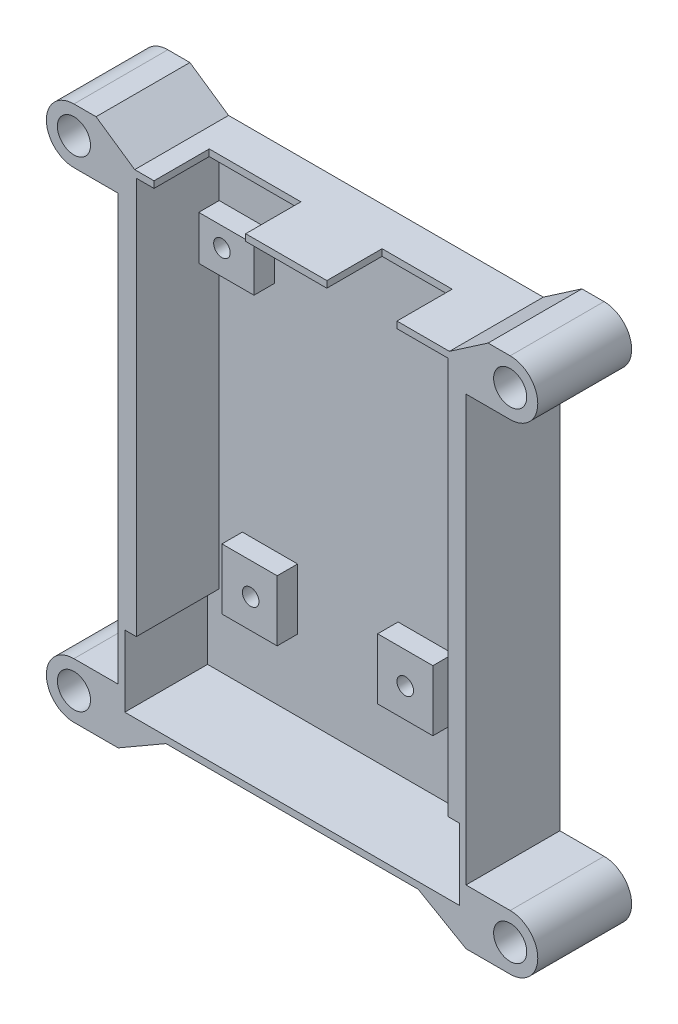
SolidWorks part; units mm, degrees
ref_plane "Front" through (0, 0, 0) normal (0, 0, 1) x (1, 0, 0)
ref_plane "Top" through (0, 0, 0) normal (0, 1, 0) x (1, 0, 0)
ref_plane "Right" through (0, 0, 0) normal (1, 0, 0) x (0, 0, -1)
sketch "草图1" plane through (0, 0, 0) normal (0, 0, 1) x (1, 0, 0)
  line L0 (0, 0) -> (8, 0)
  line L1 (8, 0) -> (8, 77)
  line L2 (8, 77) -> (0, 77)
  line L3 (0, -10) -> (8, -10)
  line L4 (8, -10) -> (16.6603, -5)
  line L5 (16.6603, -5) -> (62.3397, -5)
  line L6 (62.3397, -5) -> (71, -10)
  line L7 (71, -10) -> (79, -10)
  line L8 (79, 0) -> (71, 0)
  line L9 (71, 0) -> (71, 77)
  line L10 (71, 77) -> (79, 77)
  line L11 (0, 87) -> (79, 87)
  arc A0 (0, 0) -> (0, -10) centre (0, -5) ccw
  arc A1 (79, -10) -> (79, 0) centre (79, -5) ccw
  arc A2 (0, 77) -> (0, 87) centre (0, 82) cw
  arc A3 (79, 87) -> (79, 77) centre (79, 82) cw
  dimension "D1" = 5
  dimension "D2" = 5
  dimension "D3" = 5
  dimension "D4" = 8
  dimension "D14" = 63
  dimension "D5" = 8
  dimension "D6" = 8
  dimension "D7" = 8
  dimension "D8" = 5
  dimension "D9" = 5
  dimension "D10" = 63
  dimension "D11" = 92
  dimension "D12" = 30
  dimension "D13" = 30
extrude "凸台-拉伸1" add sketch "草图1" along normal blind 2
sketch "草图2" plane through (0, 0, 2) normal (0, 0, 1) x (1, 0, 0)
  line L0 (79, 87) -> (0, 87) construction
  line L1 (11.3, 81) -> (67.7, 81)
  line L2 (11.3, 81) -> (11.3, 9.1)
  line L3 (11.3, 9.1) -> (67.7, 9.1)
  line L4 (67.7, 81) -> (67.7, 9.1)
  point P4 (39.5, 81)
  point P7 (39.5, 87)
  arc M5 (0, 0) -> (0, -10) centre (0, -5) ccw
  line M6 (0, -10) -> (8, -10)
  line M7 (8, -10) -> (16.6603, -5)
  line M8 (16.6603, -5) -> (62.3397, -5)
  line M9 (62.3397, -5) -> (71, -10)
  line M10 (71, -10) -> (79, -10)
  arc M11 (79, -10) -> (79, 0) centre (79, -5) ccw
  line M12 (79, 0) -> (71, 0)
  line M13 (71, 0) -> (71, 77)
  line M14 (71, 77) -> (79, 77)
  arc M15 (79, 77) -> (79, 87) centre (79, 82) ccw
  line M16 (79, 87) -> (0, 87)
  arc M17 (0, 87) -> (0, 77) centre (0, 82) ccw
  line M18 (0, 77) -> (8, 77)
  line M19 (8, 77) -> (8, 0)
  line M20 (8, 0) -> (0, 0)
  dimension "D1" = 71.9
  dimension "D2" = 56.4
  dimension "D3" = 6
extrude "凸台-拉伸3" add sketch "草图2" along normal blind 15 contours L1 L4 L3 L2 M20 M5 M6 M7 M8 M9 M10 M11 M12 M13 M14 M15 M16 M17 M18 M19
sketch "草图6" plane through (0, 0, 17) normal (0, 0, 1) x (1, 0, 0)
  circle A0 centre (0, 82) radius 3
  circle A1 centre (0, -5) radius 3
  circle A2 centre (79, -5) radius 3
  circle A3 centre (79, 82) radius 3
  dimension "D1" = 6
  dimension "D2" = 6
  dimension "D3" = 6
  dimension "D4" = 6
extrude "切除-拉伸1" cut sketch "草图6" against normal through all
sketch "草图7" plane through (0, 0, 2) normal (0, 0, 1) x (1, 0, 0)
  line L0 (67.7, 61.8) -> (67.7, 69.8)
  line L1 (67.7, 61.8) -> (57.7, 61.8)
  line L2 (67.7, 69.8) -> (57.7, 69.8)
  line L3 (57.7, 61.8) -> (57.7, 69.8)
  line L4 (67.7, 81) -> (67.7, 9.1) construction
  line L5 (11.3, 62) -> (11.3, 70)
  line L6 (11.3, 62) -> (21.3, 62)
  line L7 (11.3, 70) -> (21.3, 70)
  line L8 (21.3, 62) -> (21.3, 70)
  line L9 (11.3, 81) -> (11.3, 9.1) construction
  line L10 (53.7, 9.1) -> (53.7, 20.1)
  line L11 (53.7, 9.1) -> (43.7, 9.1)
  line L12 (53.7, 20.1) -> (43.7, 20.1)
  line L13 (43.7, 9.1) -> (43.7, 20.1)
  line L14 (11.3, 9.1) -> (67.7, 9.1) construction
  line L15 (25.5, 9.1) -> (15.5, 9.1)
  line L16 (25.5, 9.1) -> (25.5, 20.1)
  line L17 (15.5, 9.1) -> (15.5, 20.1)
  line L18 (25.5, 20.1) -> (15.5, 20.1)
  line L19 (11.3, 81) -> (67.7, 81) construction
  dimension "D1" = 10
  dimension "D2" = 8
  dimension "D3" = 8
  dimension "D4" = 10
  dimension "D5" = 11
  dimension "D6" = 10
  dimension "D7" = 11
  dimension "D8" = 10
  dimension "D9" = 11.2
  dimension "D10" = 11
  dimension "D11" = 14
  dimension "D12" = 4.2
extrude "凸台-拉伸4" add sketch "草图7" along normal blind 3.7
ref_plane "基准面2" through (0, 0, 5.7) normal (0, 0, 1) x (1, 0, 0)
sketch "草图8" plane through (0, 0, 5.7) normal (0, 0, 1) x (1, 0, 0)
  line L0 (67.7, 61.8) -> (67.7, 69.8) construction
  line L1 (11.3, 81) -> (67.7, 81) construction
  line L2 (11.3, 70) -> (11.3, 62) construction
  line L3 (43.7, 9.1) -> (53.7, 9.1) construction
  line L4 (67.7, 61.8) -> (67.7, 9.1) construction
  line L5 (15.5, 9.1) -> (25.5, 9.1) construction
  line L6 (11.3, 62) -> (11.3, 9.1) construction
  circle A0 centre (63.7, 65.2) radius 1.5
  circle A1 centre (15.5, 66.5) radius 1.5
  circle A2 centre (20.7, 14.4) radius 1.5
  circle A3 centre (48.7, 14.4) radius 1.5
  dimension "D1" = 3
  dimension "D2" = 3
  dimension "D3" = 3
  dimension "D4" = 3
  dimension "D5" = 4
  dimension "D6" = 15.8
  dimension "D7" = 4.2
  dimension "D8" = 14.5
  dimension "D9" = 5.3
  dimension "D10" = 19
  dimension "D11" = 5.3
  dimension "D12" = 9.4
extrude "切除-拉伸2" cut sketch "草图8" against normal through all
sketch "草图10" plane through (0, 81, 0) normal (0, -1, 0) x (1, 0, 0)
  line L0 (14.5, 17) -> (31.1, 17)
  line L1 (14.5, 17) -> (14.5, 7)
  line L2 (31.1, 17) -> (31.1, 7)
  line L3 (14.5, 7) -> (31.1, 7)
  line L4 (11.3, 17) -> (67.7, 17) construction
  line L5 (45.8, 17) -> (58.5, 17)
  line L6 (45.8, 17) -> (45.8, 7)
  line L7 (58.5, 17) -> (58.5, 7)
  line L8 (45.8, 7) -> (58.5, 7)
  line L9 (11.3, 2) -> (67.7, 2) construction
  line L11 (67.7, 17) -> (67.7, 2) construction
  dimension "D1" = 5
  dimension "D2" = 5
  dimension "D3" = 16.6
  dimension "D4" = 12.7
  dimension "D5" = 14.7
  dimension "D6" = 9.2
sketch "草图11" plane through (0, 0, 17) normal (0, 0, 1) x (1, 0, 0)
  line L0 (4, 87) -> (11, 82.2)
  line L1 (79, 87) -> (0, 87) construction
  line L2 (11, 82.2) -> (68, 82.2)
  line L3 (68, 82.2) -> (75, 87)
  line L4 (79, 87) -> (0, 87) construction
  circle A0 centre (0, 82) radius 3 construction
  circle A1 centre (79, 82) radius 3 construction
  dimension "D1" = 11
  dimension "D2" = 11
  dimension "D3" = 7
  dimension "D4" = 7
  dimension "D5" = 4.8
extrude "切除-拉伸5" cut sketch "草图11" against normal through all and the other way through all
sketch "草图14" plane through (0, 0, 17) normal (0, 0, 1) x (1, 0, 0)
  line L0 (9.2, 9.1) -> (69.8, 9.1)
  line L1 (9.2, 9.1) -> (9.2, -3.8)
  line L2 (69.8, 9.1) -> (69.8, -3.8)
  line L3 (9.2, -3.8) -> (69.8, -3.8)
  line L4 (11.3, 9.1) -> (67.7, 9.1) construction
  line L5 (16.6603, -5) -> (62.3397, -5) construction
  line L6 (8, 77) -> (8, 0) construction
  line L7 (71, 0) -> (71, 77) construction
  dimension "D1" = 0
  dimension "D2" = 1.2
  dimension "D3" = 1.2
  dimension "D4" = 1.2
extrude "切除-拉伸10" cut sketch "草图14" against normal blind 15
extrude "切除-拉伸12" cut sketch "草图10" against normal blind 10
sketch "草图15" plane through (0, 0, 0) normal (0, 0, -1) x (-1, 0, 0)
  circle A0 centre (-15.5, 66.5) radius 2.8
  circle A1 centre (-20.7, 14.4) radius 2.8
  circle A2 centre (-48.7, 14.4) radius 2.8
  circle A3 centre (-63.7, 65.2) radius 2.8
  dimension "D1" = 5.6
  dimension "D2" = 5.6
  dimension "D3" = 5.6
  dimension "D4" = 5.6
extrude "切除-拉伸15" cut sketch "草图15" against normal blind 2.4
